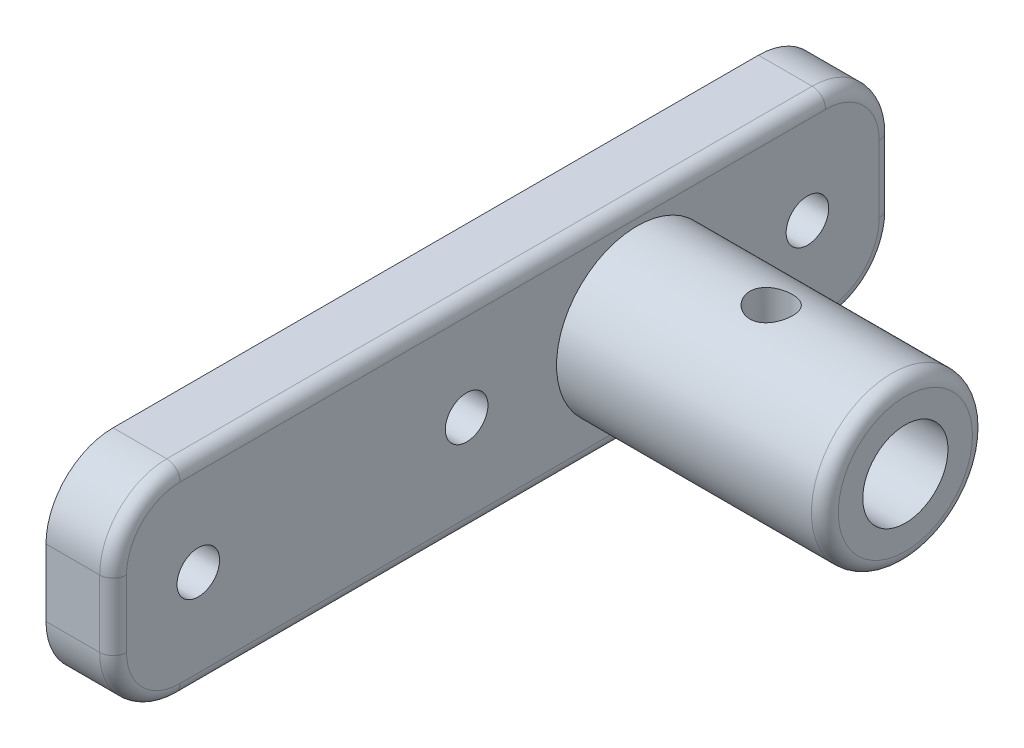
SolidWorks part; units mm, degrees
ref_plane "Front Plane" through (0, 0, 0) normal (0, 0, 1) x (1, 0, 0)
ref_plane "Top Plane" through (0, 0, 0) normal (0, 1, 0) x (1, 0, 0)
ref_plane "Right Plane" through (0, 0, 0) normal (1, 0, 0) x (0, 0, -1)
sketch "Sketch1" plane through (0, 0, 0) normal (1, 0, 0) x (0, 0, -1)
  line L0 (-24.5161, 16.3535) -> (13.5839, 16.3535) construction
  line L1 (-24.5161, 8.8535) -> (13.5839, 8.8535)
  line L2 (-24.5161, 23.8535) -> (-24.5161, 8.8535) construction
  line L3 (-24.5161, 23.8535) -> (13.5839, 23.8535)
  line L4 (13.5839, 8.8535) -> (13.5839, 23.8535)
  line L5 (-24.5161, 23.8535) -> (-44.5161, 23.8535)
  line L6 (-44.5161, 23.8535) -> (-44.5161, 8.8535)
  line L7 (-44.5161, 8.8535) -> (-24.5161, 8.8535)
  circle A0 centre (-18.1661, 16.3535) radius 1.5875
  circle A1 centre (7.2339, 16.3535) radius 1.5875
  circle A2 centre (-38.1661, 16.3535) radius 1.5875
  dimension "D5" = 3.175
  dimension "D1" = 20
  dimension "D2" = 15
  dimension "D3" = 6.35
  dimension "D4" = 25.4
  dimension "D6" = 6.35
  dimension "D7" = 6.35
extrude "Boss-Extrude1" add sketch "Sketch1" along normal blind 5
sketch "Sketch2" plane through (5, 0, 0) normal (1, 0, 0) x (0, 0, -1)
  line L0 (13.5839, 16.3535) -> (-44.5161, 16.3535) construction
  line L4 (13.5839, 8.8535) -> (13.5839, 23.8535) construction
  line L5 (-44.5161, 23.8535) -> (-44.5161, 8.8535) construction
  circle A0 centre (-5.4661, 16.3535) radius 6
  circle A1 centre (-5.4661, 16.3535) radius 3.175
  dimension "D1" = 12
extrude "Boss-Extrude2" add sketch "Sketch2" along normal blind 20
fillet "Fillet1" radius 5 4 edges at (2.5, 8.8535, -13.5839) (2.5, 23.8535, -13.5839) (2.5, 8.8535, 44.5161) (2.5, 23.8535, 44.5161)
fillet "Fillet2" radius 1 1 edges at (25, 16.3535, -0.5339)
sketch "Sketch3" plane through (0, 23.8535, 0) normal (0, 1, 0) x (1, 0, 0)
  line L0 (5, -5.4661) -> (26.1196, -5.4661) construction
  line L1 (5, 8.5839) -> (5, -39.5161) construction
  circle A0 centre (15, -5.4661) radius 1.5875
  dimension "D1" = 10
extrude "Cut-Extrude1" cut sketch "Sketch3" against normal through all
fillet "Fillet3" radius 1 8 edges at (5, 23.8535, 15.4661) (5, 22.3891, -12.1194) (5, 16.3535, -13.5839) (5, 10.318, -12.1194) (5, 8.8535, 15.4661) (5, 10.318, 43.0517) (5, 16.3535, 44.5161) (5, 22.3891, 43.0517)
sketch "Sketch4" plane through (5, 0, 0) normal (1, 0, 0) x (0, 0, -1)
  circle A0 centre (-5.4661, 16.3535) radius 3.175
extrude "Cut-Extrude2" cut sketch "Sketch4" against normal through all
